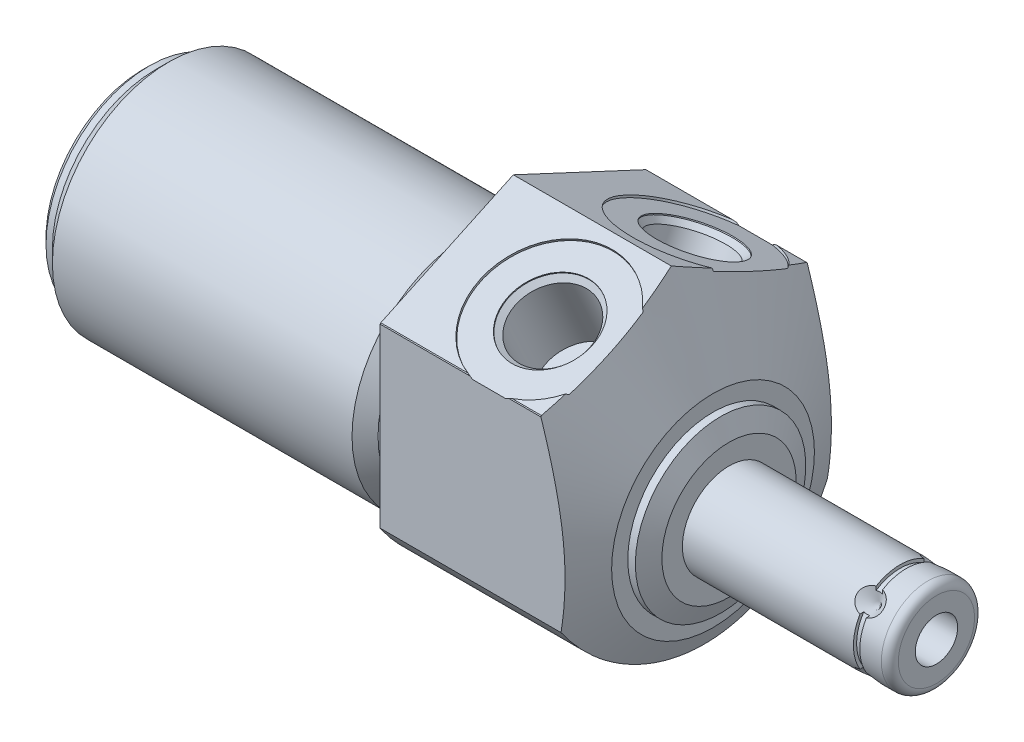
SolidWorks part; units mm, degrees
material "Alloy Steel"
ref_plane "Front Plane" through (0, 0, 0) normal (0, 0, 1) x (1, 0, 0)
ref_plane "Top Plane" through (0, 0, 0) normal (0, 1, 0) x (1, 0, 0)
ref_plane "Right Plane" through (0, 0, 0) normal (1, 0, 0) x (0, 0, -1)
sketch "Sketch1" plane through (0, 0, 0) normal (1, 0, 0) x (0, 0, -1)
  circle A0 centre (0, 0) radius 25.4
  dimension "D1" = 50.8
extrude "Extrude1" add sketch "Sketch1" along normal blind 25.7048 and the other way blind 44.1452
sketch "Sketch2" plane through (0, 0, 0) normal (1, 0, 0) x (0, 0, -1)
  line L0 (-14.6964, -4.7498) -> (14.6964, -4.7498) construction
  circle A0 centre (0, -4.7498) radius 13.8684
  circle A1 centre (0, 0) radius 25.4 construction
  circle A2 centre (0, 0) radius 25.4
  dimension "D1" = 27.7368
  dimension "D2" = 4.7498
extrude "Cut-Extrude1" cut sketch "Sketch2" against normal up to next
sketch "Sketch4" plane through (25.7048, 0, 0) normal (-1, 0, 0) x (0, 0, 1)
  line L0 (15.875, -10.5303) -> (15.875, 10.5303)
  line L1 (15.8029, 10.6381) -> (0, 18.0071)
  line L2 (-15.875, -10.5303) -> (-15.875, 10.5303)
  line L3 (-15.8029, 10.6381) -> (0, 18.0071)
  line L4 (0, -20.9029) -> (0, 19.86) construction
  circle A0 centre (0, 0) radius 25.4 construction
  circle A1 centre (0, 0) radius 25.4
  arc A2 (-15.8029, 10.6381) -> (-15.875, 10.5303) centre (0, 0) ccw
  arc A3 (-15.875, -10.5303) -> (15.875, -10.5303) centre (0, 0) ccw
  arc A4 (15.875, 10.5303) -> (15.8029, 10.6381) centre (0, 0) ccw
  dimension "D4" = 19.05
  dimension "D1" = 31.75
  dimension "D2" = 65
  dimension "D3" = 20.6248
extrude "Cut-Extrude3" cut sketch "Sketch4" along normal up to next
sketch "Sketch6" plane through (0, 0, 0) normal (0, 0, 1) x (1, 0, 0)
  line L0 (18.824, 18.0071) -> (23.7998, 7.3365)
  line L1 (1.9872, -4.7498) -> (19.8625, -4.7498) construction
  line L2 (-44.1452, -4.7498) -> (0, -4.7498) construction
  line L3 (25.7048, 18.0071) -> (25.7048, 10.6381) construction
  line L4 (25.7048, 3.2512) -> (25.7048, 18.0071)
  line L5 (25.7048, 18.0071) -> (18.824, 18.0071)
  line L6 (25.7048, 18.0071) -> (0, 18.0071) construction
  line L7 (23.7998, 7.3365) -> (23.7998, 5.4102)
  line L8 (23.7998, 5.4102) -> (24.698, 5.4102)
  line L9 (24.698, 5.4102) -> (25.7048, 3.2512)
  line L10 (0, 9.1186) -> (0, -18.6182) construction
  dimension "D1" = 16.002
  dimension "D2" = 25
  dimension "D3" = 20.32
  dimension "D4" = 23.7998
revolve "Cut-Revolve2" cut sketch "Sketch6" angle 360 about L1
ref_plane "Plane17" through (13.0048, 0, 0) normal (-1, 0, 0) x (0, 0, 1)
sketch "S2D0002" plane through (13.0048, 13.7124, 8.6091) normal (1, 0, 0) x (0, 0.4226, -0.9063)
  line L0 (5.0165, 0) -> (8.255, 0)
  line L1 (5.0165, 0) -> (5.0165, -0.127)
  line L2 (5.0165, -0.127) -> (4.4196, -0.7239)
  line L3 (4.4196, -0.7239) -> (4.4196, -9.398)
  line L4 (4.4196, -9.398) -> (0, -9.398)
  line L5 (0, -9.398) -> (0, 0.254)
  line L6 (0, -12.8016) -> (0, 0.6096) construction
  line L7 (8.255, 0.254) -> (8.255, 0)
  line L8 (9.6175, 0.254) -> (-7.8191, 0.254) construction
  line L9 (8.255, 0.254) -> (0, 0.254)
  dimension "D1" = 16.51
  dimension "D2" = 0.254
  dimension "D3" = 0.127
  dimension "D4" = 10.033
  dimension "D5" = 45
  dimension "D6" = 8.8392
  dimension "D7" = 9.398
revolve "Cut-Revolve3" cut sketch "S2D0002" angle 360 about L6
mirror "Mirror1" about plane through (0, 0, 0) normal (0, 0, 1) of "Cut-Revolve3"
sketch "Sketch10" plane through (0, 0, 0) normal (0, 0, 1) x (1, 0, 0)
  line L0 (0, 9.1186) -> (0, 7.5692)
  line L1 (0, 7.5692) -> (-3.81, 7.5692)
  line L2 (-3.81, 7.5692) -> (-5.3594, 9.1186)
  line L3 (-5.094, -4.7498) -> (0.2426, -4.7498) construction
  line L4 (0, 9.1186) -> (-5.3594, 9.1186)
  line L5 (-44.1452, -4.7498) -> (0, -4.7498) construction
  line L6 (0, 9.1186) -> (-44.1452, 9.1186) construction
  line L7 (0, 10.5303) -> (0, -10.5303) construction
  dimension "D1" = 24.638
  dimension "D2" = 3.81
  dimension "D3" = 45
revolve "Cut-Revolve6" cut sketch "Sketch10" angle 360 about L3
sketch "Sketch12" plane through (0, 0, 0) normal (0, 0, 1) x (1, 0, 0)
  line L0 (-44.1452, 9.1186) -> (-44.1452, 7.5692)
  line L1 (-44.1452, 7.5692) -> (-42.6212, 7.5692)
  line L2 (-42.6212, 7.5692) -> (-41.0718, 9.1186)
  line L3 (-50.9283, -4.7498) -> (-48.1063, -4.7498) construction
  line L4 (-44.1452, 9.1186) -> (-41.0718, 9.1186)
  line L5 (-44.1452, -4.7498) -> (-5.3594, -4.7498) construction
  line L6 (-5.3594, 9.1186) -> (-44.1452, 9.1186) construction
  line L7 (-44.1452, 9.1186) -> (-44.1452, -18.6182) construction
  dimension "D1" = 24.638
  dimension "D2" = 1.524
  dimension "D3" = 45
revolve "Cut-Revolve8" cut sketch "Sketch12" angle 360 about L3
chamfer "Chamfer1" distance 0.762 angle 45 1 edges at (-44.1452, -4.7498, 12.319)
sketch "Sketch13" plane through (0, 0, 0) normal (0, 0, 1) x (1, 0, 0)
  line L0 (25.7048, -4.7498) -> (50.432, -4.7498)
  line L1 (50.432, -4.7498) -> (50.432, -9.29)
  line L2 (49.416, -10.3061) -> (25.7048, -10.306)
  line L3 (25.7048, -10.306) -> (25.7048, -4.7498)
  line L4 (4.7498, -4.7498) -> (27.0459, -4.7498) construction
  line L5 (-41.0718, -4.7498) -> (-5.3594, -4.7498) construction
  line L6 (25.7048, -12.7508) -> (25.7048, 3.2512) construction
  line L7 (0, 10.5303) -> (0, -10.5303) construction
  arc A0 (49.416, -10.3061) -> (50.432, -9.29) centre (49.416, -9.29) ccw
  dimension "D2" = 1.016
  dimension "D1" = 50.432
  dimension "D3" = 11.1125
revolve "Revolve1" add sketch "Sketch13" angle 360 about L4
ref_plane "Plane18" through (0, -2.3749, -2.3749) normal (0, 0.7071, 0.7071) x (-1, 0, 0)
sketch "S2D0001" plane through (0, 0, 0) normal (0, 0, 1) x (1, 0, 0)
  line L0 (50.432, -2.2225) -> (40.272, -2.2225)
  line L1 (40.272, -2.2225) -> (38.7534, -4.7498)
  line L2 (50.432, -2.2225) -> (50.432, -4.7498)
  line L3 (50.432, -4.7498) -> (38.7534, -4.7498)
  line L4 (-2.8067, -4.7498) -> (-15.8378, -4.7498) construction
  line L5 (49.416, -4.7498) -> (25.7048, -4.7498) construction
  line L6 (50.432, -9.29) -> (50.432, -0.2096) construction
  dimension "D1" = 5.0546
  dimension "D2" = 10.16
  dimension "D3" = 59
revolve "Cut-Revolve9" cut sketch "S2D0001" angle 360 about L4
sketch "Sketch16" plane through (0, -8.1084, 3.3586) normal (0, -0.7071, -0.7071) x (1, 0, 0)
  line L0 (46.4696, -10.306) -> (44.8821, -10.306)
  line L1 (44.8821, -10.306) -> (46.4696, -8.7185)
  line L2 (46.4696, -10.306) -> (46.4696, -8.7185)
  line L3 (46.4696, -3.4788) -> (46.4696, 0.0794) construction
  line L4 (50.432, -9.2901) -> (50.432, -0.2096) construction
  line L5 (25.7048, -10.3061) -> (49.416, -10.3061) construction
  dimension "D1" = 3.9624
  dimension "D2" = 3.175
  dimension "D3" = 45
revolve "Cut-Revolve10" cut sketch "Sketch16" angle 360 about L3
pattern_circular "CirPattern1" count 4 over 360 about axis through (4.7498, -4.7498, 0) along (-1, 0, 0) of "Cut-Revolve10"
sketch "Sketch21" plane through (0, 0, 0) normal (0, 0, 1) x (1, 0, 0)
  line L1 (46.0886, 0.8065) -> (46.8506, 0.8065)
  line L2 (46.0886, 0.8065) -> (46.0886, 0.4255)
  line L3 (46.0886, 0.4255) -> (46.8506, 0.4255)
  line L4 (46.8506, 0.8065) -> (46.8506, 0.4255)
  line L5 (46.4696, -0.7782) -> (46.4696, 2.3032) construction
  line L7 (23.8735, -4.7498) -> (50.6625, -4.7498) construction
  line L10 (50.432, -9.29) -> (50.432, -0.2096) construction
  line L11 (52.5657, -4.7498) -> (43.1167, -4.7498) construction
  dimension "D1" = 0.381
  dimension "D2" = 0.762
  dimension "D3" = 3.5814
  dimension "D4" = 5.5562
revolve "Cut-Revolve11" cut sketch "Sketch21" angle 360 about L7
